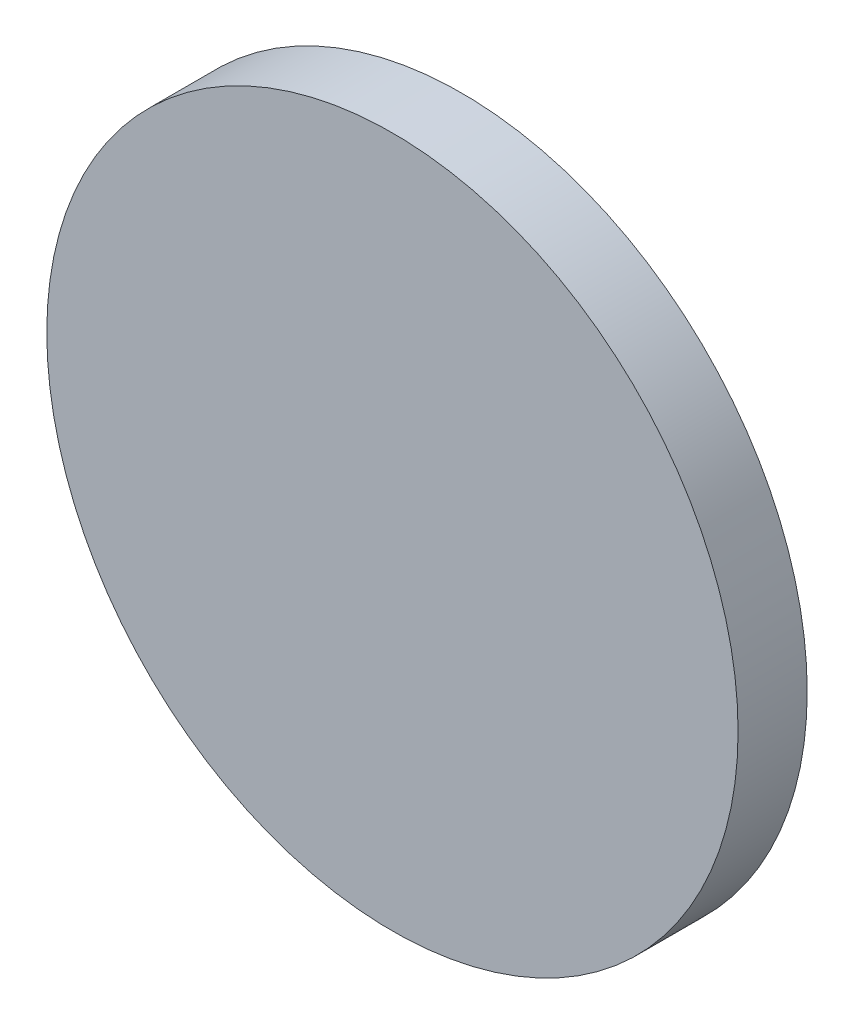
SolidWorks part; units mm, degrees
material "Glass"
ref_plane "Front Plane" through (0, 0, 0) normal (0, 0, 1) x (1, 0, 0)
ref_plane "Top Plane" through (0, 0, 0) normal (0, 1, 0) x (1, 0, 0)
ref_plane "Right Plane" through (0, 0, 0) normal (1, 0, 0) x (0, 0, -1)
sketch "Sketch1" plane through (0, 0, 0) normal (0, 0, 1) x (1, 0, 0)
  circle A0 centre (0, 0) radius 31.75
  dimension "D1" = 63.5
extrude "Boss-Extrude1" add sketch "Sketch1" along normal blind 6.35
